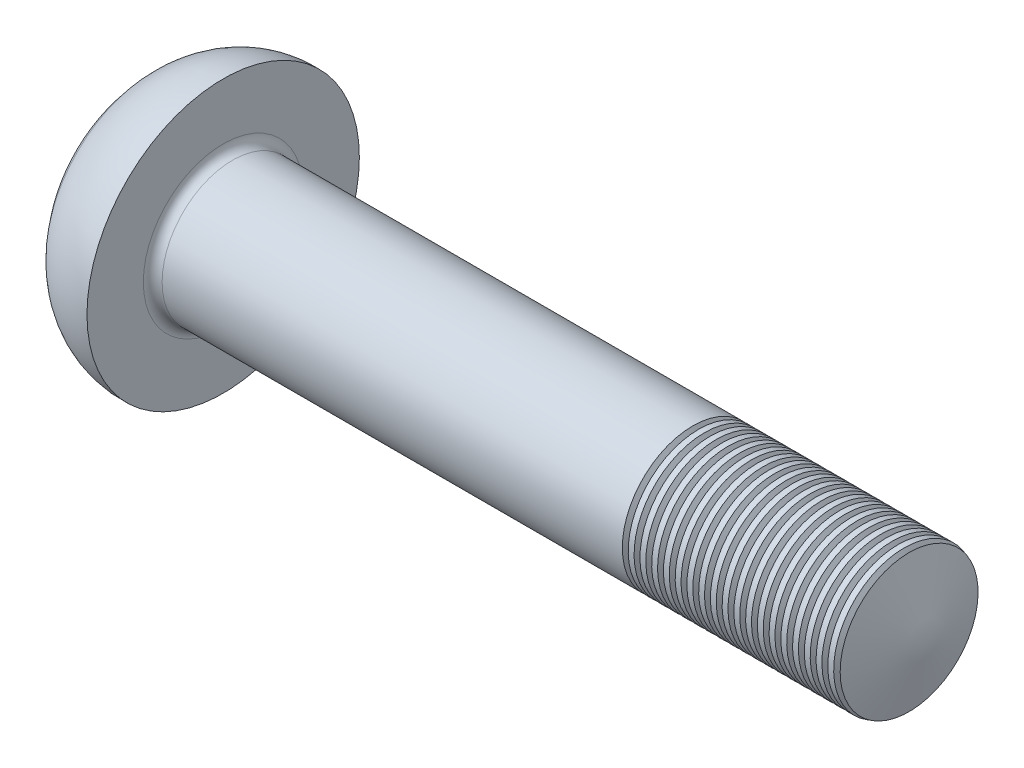
SolidWorks part; units mm, degrees
ref_plane "Front" through (0, 0, 0) normal (0, 0, 1) x (1, 0, 0)
ref_plane "Top" through (0, 0, 0) normal (0, 1, 0) x (1, 0, 0)
ref_plane "Right" through (0, 0, 0) normal (1, 0, 0) x (0, 0, -1)
sketch "Sketch1" plane through (0, 0, 0) normal (0, 1, 0) x (1, 0, 0)
  line L0 (-13.6293, 0) -> (11.3577, 0) construction
  line L1 (2.37, 1.5) -> (17.37, 1.5)
  line L2 (17.37, 1.5) -> (17.37, 0)
  line L3 (2.37, 1.5) -> (2.37, 2.9)
  line L4 (17.37, 0) -> (0, 0)
  arc A0 (2.37, 2.9) -> (0.8698, 2.2711) centre (2.2837, 1.002) ccw
  arc A1 (0, 0) -> (0.8698, 2.2711) centre (3.4, 0) cw
  dimension "r2" = 1.9
  dimension "r1" = 3.4
  dimension "d" = 3
  dimension "dk" = 5.8
  dimension "k" = 2.37
  dimension "l" = 15
revolve "Revolve1" add sketch "Sketch1" angle 360 about L0
cosmetic thread "ThreadCosmetic1" parameters "l0"=3.5, "dm"=2.75
fillet "Fillet2" radius 0.2 1 edges at (2.37, 0, 1.5)
sketch "Sketch4" plane through (0, 0, 0) normal (0, 1, 0) x (1, 0, 0)
  line L0 (4.7828, 0) -> (7.1391, 0) construction
  line L2 (18.1035, 0) -> (18.1035, 21)
  line L3 (18.1035, 21) -> (11.7431, 21)
  line L4 (11.7431, 21) -> (17.37, 0)
  line L5 (17.37, 0) -> (18.1035, 0)
  line L7 (17.37, -1.5) -> (17.37, 1.5) construction
  dimension "D1" = 75
  dimension "D2" = 0.7335
  dimension "D3" = 21
revolve "Cut-Revolve1" cut sketch "Sketch4" angle 360 about L0
sketch "Sketch2" plane through (0, 0, 0) normal (1, 0, 0) x (0, 0, -1)
  line L0 (-2.278, 0) -> (2.6944, 0) construction
  line L1 (0, -2.1234) -> (0, 2.1948) construction
  line L2 (-0.4625, 0.4625) -> (-1.85, 0.4625)
  line L3 (0.4625, -1.85) -> (-0.4625, -1.85)
  line L4 (0.4625, -1.85) -> (0.4625, -0.4625)
  line L5 (0.4625, 1.85) -> (-0.4625, 1.85)
  line L6 (-0.4625, -1.85) -> (-0.4625, -0.4625)
  line L7 (1.85, 0.4625) -> (0.4625, 0.4625)
  line L8 (1.85, 0.4625) -> (1.85, -0.4625)
  line L9 (1.85, -0.4625) -> (0.4625, -0.4625)
  line L10 (-1.85, 0.4625) -> (-1.85, -0.4625)
  line L11 (-0.4625, 0.4625) -> (-0.4625, 1.85)
  line L12 (-0.4625, -0.4625) -> (-1.85, -0.4625)
  line L13 (0.4625, 0.4625) -> (0.4625, 1.85)
  point P19 (-0.4625, 0.4625)
  point P22 (0.4625, 0.4625)
  point P27 (-0.4625, -0.4625)
  dimension "m" = 3.7
  dimension "D2" = 3.7
  dimension "D3" = 0.925
  dimension "D4" = 0.925
ref_plane "Plane1" through (2.62, 0, 0) normal (1, 0, 0) x (0, 0, -1)
sketch "Sketch5" plane through (2.62, 0, 0) normal (1, 0, 0) x (0, 0, -1)
  point P0 (0, 0)
loft "Cut-Loft1" cut profiles "Sketch5", "Sketch2"
sketch "Sketch6" plane through (0, 0, 0) normal (0, 0, 1) x (1, 0, 0)
  line L0 (12.37, 1.7) -> (12.495, 1.7)
  line L1 (12.495, 1.7) -> (12.495, 1.5)
  line L2 (12.495, 1.5) -> (12.4325, 1.3917)
  line L3 (12.37, 1.5) -> (12.4325, 1.3917)
  line L4 (12.37, 1.7) -> (12.37, 1.5)
  line L5 (10.7743, 0) -> (0, 0) construction
  line L6 (12.37, 1.5) -> (12.495, 1.5) construction
  line L7 (12.4325, 1.5) -> (12.4325, 1.3917) construction
  line L8 (16.9681, 1.5) -> (2.57, 1.5) construction
  point P5 (12.4325, 1.7)
  dimension "D1" = 0.2
  dimension "D2" = 0.125
  dimension "D3" = 5
revolve "Cut-Revolve10" cut sketch "Sketch6" angle 360 about L5
pattern_linear "LPattern10" count 20 spacing 0.25 along (1, 0, 0) of "Cut-Revolve10"
equation "\"D4@Sketch2\" = \"D3@Sketch2\""
equation "\"D2@Sketch2\" = \"m@Sketch2\""
equation "\"D3@Sketch2\" = \"m@Sketch2\" / 4"
equation "\"D2@Sketch6\" = (  \"d@Sketch1\" - \"dm@ThreadCosmetic1\" )  / 2"
equation "\"D3@Sketch6\" = \"l0@ThreadCosmetic1\" + \"d@Sketch1\" / 2"
equation "\"D3@LPattern10\" = \"D2@Sketch6\" *2"
equation "\"D1@LPattern10\" = \"D3@Sketch6\" / \"D3@LPattern10\""
